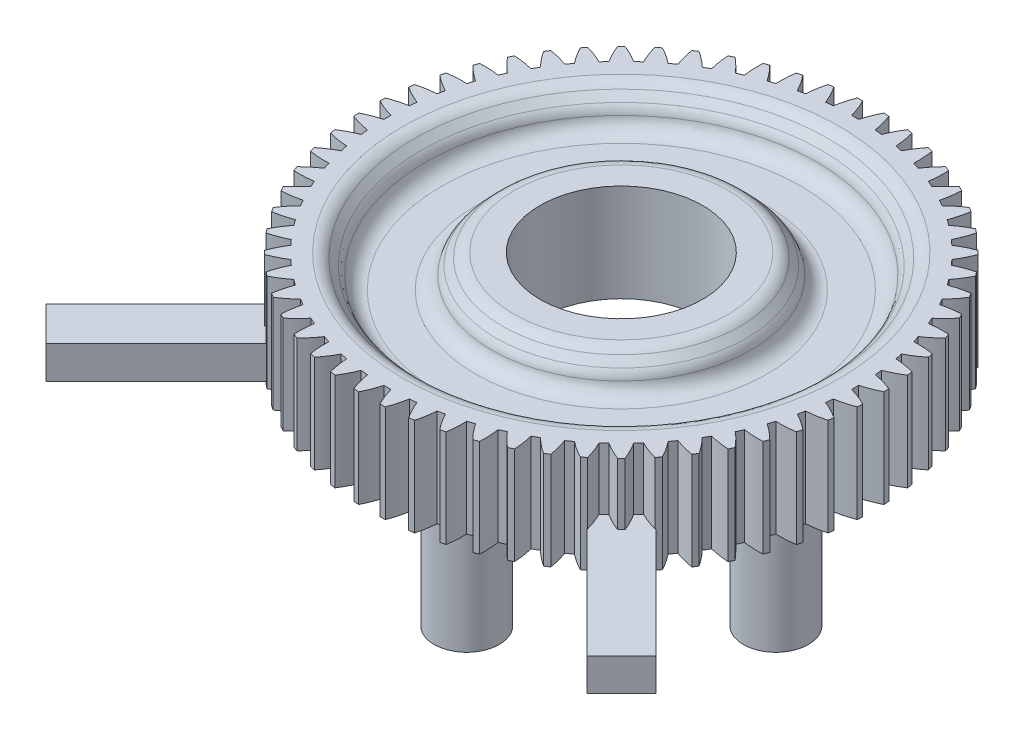
SolidWorks part; units mm, degrees
ref_plane "Front" through (0, 0, 0) normal (0, 0, 1) x (1, 0, 0)
ref_plane "Top" through (0, 0, 0) normal (0, 1, 0) x (1, 0, 0)
ref_plane "Right" through (0, 0, 0) normal (1, 0, 0) x (0, 0, -1)
sketch "Sketch1" plane through (0, 0, 0) normal (0, 1, 0) x (1, 0, 0)
  arc A240 (-0.2149, 14.3725) -> (-0.65, 15.4864) centre (-5.9935, 12.7577) ccw
  arc A241 (-0.65, 15.4864) -> (-0.9723, 15.4695) centre (0, 0.0001) ccw
  arc A242 (-0.9723, 15.4695) -> (-1.2885, 14.3162) centre (4.6272, 13.3143) ccw
  arc A243 (-1.2885, 14.3162) -> (-1.7161, 14.2713) centre (0, 0.0001) ccw
  arc A244 (-1.7161, 14.2713) -> (-2.2652, 15.3337) centre (-7.2942, 12.0613) ccw
  arc A245 (-2.2652, 15.3337) -> (-2.584, 15.2832) centre (0, 0.0001) ccw
  arc A246 (-2.584, 15.2832) -> (-2.7779, 14.1031) centre (3.2101, 13.725) ccw
  arc A247 (-2.7779, 14.1031) -> (-3.1984, 14.0137) centre (0, 0.0001) ccw
  arc A248 (-3.1984, 14.0137) -> (-3.8555, 15.0129) centre (-8.515, 11.2328) ccw
  arc A249 (-3.8555, 15.0129) -> (-4.1674, 14.9293) centre (0, 0.0001) ccw
  arc A250 (-4.1674, 14.9293) -> (-4.2369, 13.7354) centre (1.7579, 13.9854) ccw
  arc A251 (-4.2369, 13.7354) -> (-4.6457, 13.6026) centre (0, 0.0001) ccw
  arc A252 (-4.6457, 13.6026) -> (-5.4037, 14.5276) centre (-9.6425, 10.2812) ccw
  arc A253 (-5.4037, 14.5276) -> (-5.7051, 14.4119) centre (0, 0.0001) ccw
  arc A254 (-5.7051, 14.4119) -> (-5.6494, 13.2173) centre (0.2864, 14.0925) ccw
  arc A255 (-5.6494, 13.2173) -> (-6.0421, 13.0425) centre (0, 0.0001) ccw
  arc A256 (-6.0421, 13.0425) -> (-6.8926, 13.8832) centre (-10.6644, 9.2169) ccw
  arc A257 (-6.8926, 13.8832) -> (-7.1803, 13.7366) centre (0, 0.0001) ccw
  arc A258 (-7.1803, 13.7366) -> (-7, 12.5544) centre (-1.1882, 14.0453) ccw
  arc A259 (-7, 12.5544) -> (-7.3723, 12.3395) centre (0, 0.0001) ccw
  arc A260 (-7.3723, 12.3395) -> (-8.3061, 13.0867) centre (-11.5694, 8.0517) ccw
  arc A261 (-8.3061, 13.0867) -> (-8.5768, 12.9108) centre (0, 0.0001) ccw
  arc A262 (-8.5768, 12.9108) -> (-8.274, 11.7539) centre (-2.6498, 13.8441) ccw
  arc A263 (-8.274, 11.7539) -> (-8.6218, 11.5012) centre (0, 0.0001) ccw
  arc A264 (-8.6218, 11.5012) -> (-9.6285, 12.1468) centre (-12.3476, 6.7983) ccw
  arc A265 (-9.6285, 12.1468) -> (-9.8794, 11.9436) centre (0, 0.0001) ccw
  arc A266 (-9.8794, 11.9436) -> (-9.4573, 10.8247) centre (-4.0824, 13.4913) ccw
  arc A267 (-9.4573, 10.8247) -> (-9.7767, 10.537) centre (0, 0.0001) ccw
  arc A268 (-9.7767, 10.537) -> (-10.8454, 11.0738) centre (-12.9906, 5.4704) ccw
  arc A269 (-10.8454, 11.0738) -> (-11.0737, 10.8455) centre (0, 0.0001) ccw
  arc A270 (-11.0737, 10.8455) -> (-10.5369, 9.7768) centre (-5.4703, 12.9907) ccw
  arc A271 (-10.5369, 9.7768) -> (-10.8246, 9.4573) centre (0, 0.0001) ccw
  arc A272 (-10.8246, 9.4573) -> (-11.9435, 9.8794) centre (-13.4912, 4.0825) ccw
  arc A273 (-11.9435, 9.8794) -> (-12.1467, 9.6286) centre (0, 0.0001) ccw
  arc A274 (-12.1467, 9.6286) -> (-11.5012, 8.6218) centre (-6.7982, 12.3477) ccw
  arc A275 (-11.5012, 8.6218) -> (-11.7538, 8.2741) centre (0, 0.0001) ccw
  arc A276 (-11.7538, 8.2741) -> (-12.9108, 8.5769) centre (-13.8441, 2.6499) ccw
  arc A277 (-12.9108, 8.5769) -> (-13.0866, 8.3061) centre (0, 0.0001) ccw
  arc A278 (-13.0866, 8.3061) -> (-12.3394, 7.3724) centre (-8.0516, 11.5695) ccw
  arc A279 (-12.3394, 7.3724) -> (-12.5543, 7.0001) centre (0, 0.0001) ccw
  arc A280 (-12.5543, 7.0001) -> (-13.7366, 7.1804) centre (-14.0452, 1.1883) ccw
  arc A281 (-13.7366, 7.1804) -> (-13.8831, 6.8927) centre (0, 0.0001) ccw
  arc A282 (-13.8831, 6.8927) -> (-13.0424, 6.0422) centre (-9.2169, 10.6645) ccw
  arc A283 (-13.0424, 6.0422) -> (-13.2172, 5.6495) centre (0, 0.0001) ccw
  arc A284 (-13.2172, 5.6495) -> (-14.4118, 5.7052) centre (-14.0925, -0.2863) ccw
  arc A285 (-14.4118, 5.7052) -> (-14.5275, 5.4038) centre (0, 0.0001) ccw
  arc A286 (-14.5275, 5.4038) -> (-13.6025, 4.6458) centre (-10.2811, 9.6426) ccw
  arc A287 (-13.6025, 4.6458) -> (-13.7354, 4.237) centre (0, 0.0001) ccw
  arc A288 (-13.7354, 4.237) -> (-14.9292, 4.1675) centre (-13.9853, -1.7578) ccw
  arc A289 (-14.9292, 4.1675) -> (-15.0128, 3.8556) centre (0, 0.0001) ccw
  arc A290 (-15.0128, 3.8556) -> (-14.0136, 3.1985) centre (-11.2327, 8.5151) ccw
  arc A291 (-14.0136, 3.1985) -> (-14.103, 2.778) centre (0, 0.0001) ccw
  arc A292 (-14.103, 2.778) -> (-15.2831, 2.5841) centre (-13.725, -3.2101) ccw
  arc A293 (-15.2831, 2.5841) -> (-15.3336, 2.2652) centre (0, 0.0001) ccw
  arc A294 (-15.3336, 2.2652) -> (-14.2712, 1.7161) centre (-12.0612, 7.2943) ccw
  arc A295 (-14.2712, 1.7161) -> (-14.3161, 1.2886) centre (0, 0.0001) ccw
  arc A296 (-14.3161, 1.2886) -> (-15.4695, 0.9724) centre (-13.3142, -4.6271) ccw
  arc A297 (-15.4695, 0.9724) -> (-15.4863, 0.65) centre (0, 0.0001) ccw
  arc A298 (-15.4863, 0.65) -> (-14.3724, 0.215) centre (-12.7576, 5.9936) ccw
  arc A299 (-14.3724, 0.215) -> (-14.3724, -0.2149) centre (0, 0.0001) ccw
  arc A300 (-14.3724, -0.2149) -> (-15.4863, -0.6499) centre (-12.7576, -5.9935) ccw
  arc A301 (-15.4863, -0.6499) -> (-15.4695, -0.9723) centre (0, 0.0001) ccw
  arc A302 (-15.4695, -0.9723) -> (-14.3161, -1.2885) centre (-13.3142, 4.6273) ccw
  arc A303 (-14.3161, -1.2885) -> (-14.2712, -1.716) centre (0, 0.0001) ccw
  arc A304 (-14.2712, -1.716) -> (-15.3336, -2.2651) centre (-12.0612, -7.2942) ccw
  arc A305 (-15.3336, -2.2651) -> (-15.2831, -2.584) centre (0, 0.0001) ccw
  arc A306 (-15.2831, -2.584) -> (-14.103, -2.7779) centre (-13.725, 3.2102) ccw
  arc A307 (-14.103, -2.7779) -> (-14.0136, -3.1984) centre (0, 0.0001) ccw
  arc A308 (-14.0136, -3.1984) -> (-15.0128, -3.8555) centre (-11.2327, -8.515) ccw
  arc A309 (-15.0128, -3.8555) -> (-14.9292, -4.1673) centre (0, 0.0001) ccw
  arc A310 (-14.9292, -4.1673) -> (-13.7354, -4.2368) centre (-13.9853, 1.758) ccw
  arc A311 (-13.7354, -4.2368) -> (-13.6025, -4.6457) centre (0, 0.0001) ccw
  arc A312 (-13.6025, -4.6457) -> (-14.5275, -5.4036) centre (-10.2811, -9.6425) ccw
  arc A313 (-14.5275, -5.4036) -> (-14.4118, -5.705) centre (0, 0.0001) ccw
  arc A314 (-14.4118, -5.705) -> (-13.2172, -5.6494) centre (-14.0925, 0.2865) ccw
  arc A315 (-13.2172, -5.6494) -> (-13.0424, -6.0421) centre (0, 0.0001) ccw
  arc A316 (-13.0424, -6.0421) -> (-13.8831, -6.8926) centre (-9.2169, -10.6643) ccw
  arc A317 (-13.8831, -6.8926) -> (-13.7366, -7.1802) centre (0, 0.0001) ccw
  arc A318 (-13.7366, -7.1802) -> (-12.5543, -7) centre (-14.0452, -1.1882) ccw
  arc A319 (-12.5543, -7) -> (-12.3394, -7.3723) centre (0, 0.0001) ccw
  arc A320 (-12.3394, -7.3723) -> (-13.0866, -8.306) centre (-8.0516, -11.5693) ccw
  arc A321 (-13.0866, -8.306) -> (-12.9108, -8.5768) centre (0, 0.0001) ccw
  arc A322 (-12.9108, -8.5768) -> (-11.7538, -8.2739) centre (-13.8441, -2.6498) ccw
  arc A323 (-11.7538, -8.2739) -> (-11.5012, -8.6217) centre (0, 0.0001) ccw
  arc A324 (-11.5012, -8.6217) -> (-12.1467, -9.6284) centre (-6.7982, -12.3476) ccw
  arc A325 (-12.1467, -9.6284) -> (-11.9435, -9.8793) centre (0, 0.0001) ccw
  arc A326 (-11.9435, -9.8793) -> (-10.8246, -9.4572) centre (-13.4912, -4.0824) ccw
  arc A327 (-10.8246, -9.4572) -> (-10.5369, -9.7767) centre (0, 0.0001) ccw
  arc A328 (-10.5369, -9.7767) -> (-11.0737, -10.8454) centre (-5.4703, -12.9905) ccw
  arc A329 (-11.0737, -10.8454) -> (-10.8454, -11.0736) centre (0, 0.0001) ccw
  arc A330 (-10.8454, -11.0736) -> (-9.7767, -10.5369) centre (-12.9906, -5.4702) ccw
  arc A331 (-9.7767, -10.5369) -> (-9.4573, -10.8245) centre (0, 0.0001) ccw
  arc A332 (-9.4573, -10.8245) -> (-9.8794, -11.9435) centre (-4.0824, -13.4912) ccw
  arc A333 (-9.8794, -11.9435) -> (-9.6285, -12.1466) centre (0, 0.0001) ccw
  arc A334 (-9.6285, -12.1466) -> (-8.6218, -11.5011) centre (-12.3476, -6.7981) ccw
  arc A335 (-8.6218, -11.5011) -> (-8.274, -11.7538) centre (0, 0.0001) ccw
  arc A336 (-8.274, -11.7538) -> (-8.5768, -12.9107) centre (-2.6498, -13.844) ccw
  arc A337 (-8.5768, -12.9107) -> (-8.3061, -13.0865) centre (0, 0.0001) ccw
  arc A338 (-8.3061, -13.0865) -> (-7.3723, -12.3393) centre (-11.5694, -8.0516) ccw
  arc A339 (-7.3723, -12.3393) -> (-7, -12.5543) centre (0, 0.0001) ccw
  arc A340 (-7, -12.5543) -> (-7.1803, -13.7365) centre (-1.1882, -14.0452) ccw
  arc A341 (-7.1803, -13.7365) -> (-6.8926, -13.8831) centre (0, 0.0001) ccw
  arc A342 (-6.8926, -13.8831) -> (-6.0421, -13.0423) centre (-10.6644, -9.2168) ccw
  arc A343 (-6.0421, -13.0423) -> (-5.6494, -13.2172) centre (0, 0.0001) ccw
  arc A344 (-5.6494, -13.2172) -> (-5.7051, -14.4118) centre (0.2864, -14.0924) ccw
  arc A345 (-5.7051, -14.4118) -> (-5.4037, -14.5275) centre (0, 0.0001) ccw
  arc A346 (-5.4037, -14.5275) -> (-4.6457, -13.6025) centre (-9.6425, -10.281) ccw
  arc A347 (-4.6457, -13.6025) -> (-4.2369, -13.7353) centre (0, 0.0001) ccw
  arc A348 (-4.2369, -13.7353) -> (-4.1674, -14.9292) centre (1.7579, -13.9853) ccw
  arc A349 (-4.1674, -14.9292) -> (-3.8555, -15.0127) centre (0, 0.0001) ccw
  arc A350 (-3.8555, -15.0127) -> (-3.1984, -14.0136) centre (-8.515, -11.2326) ccw
  arc A351 (-3.1984, -14.0136) -> (-2.7779, -14.1029) centre (0, 0.0001) ccw
  arc A352 (-2.7779, -14.1029) -> (-2.584, -15.283) centre (3.2101, -13.7249) ccw
  arc A353 (-2.584, -15.283) -> (-2.2652, -15.3335) centre (0, 0.0001) ccw
  arc A354 (-2.2652, -15.3335) -> (-1.7161, -14.2711) centre (-7.2942, -12.0612) ccw
  arc A355 (-1.7161, -14.2711) -> (-1.2885, -14.3161) centre (0, 0.0001) ccw
  arc A356 (-1.2885, -14.3161) -> (-0.9723, -15.4694) centre (4.6272, -13.3142) ccw
  arc A357 (-0.9723, -15.4694) -> (-0.65, -15.4863) centre (0, 0.0001) ccw
  arc A358 (-0.65, -15.4863) -> (-0.2149, -14.3723) centre (-5.9935, -12.7576) ccw
  arc A359 (-0.2149, -14.3723) -> (0.215, -14.3723) centre (0, 0.0001) ccw
  arc A360 (0.215, -14.3723) -> (0.65, -15.4863) centre (5.9936, -12.7576) ccw
  arc A361 (0.65, -15.4863) -> (0.9724, -15.4694) centre (0, 0.0001) ccw
  arc A362 (0.9724, -15.4694) -> (1.2886, -14.3161) centre (-4.6272, -13.3142) ccw
  arc A363 (1.2886, -14.3161) -> (1.7161, -14.2711) centre (0, 0.0001) ccw
  arc A364 (1.7161, -14.2711) -> (2.2652, -15.3335) centre (7.2943, -12.0612) ccw
  arc A365 (2.2652, -15.3335) -> (2.584, -15.283) centre (0, 0.0001) ccw
  arc A366 (2.584, -15.283) -> (2.778, -14.1029) centre (-3.2101, -13.7249) ccw
  arc A367 (2.778, -14.1029) -> (3.1984, -14.0136) centre (0, 0.0001) ccw
  arc A368 (3.1984, -14.0136) -> (3.8556, -15.0127) centre (8.5151, -11.2326) ccw
  arc A369 (3.8556, -15.0127) -> (4.1674, -14.9292) centre (0, 0.0001) ccw
  arc A370 (4.1674, -14.9292) -> (4.2369, -13.7353) centre (-1.7579, -13.9853) ccw
  arc A371 (4.2369, -13.7353) -> (4.6457, -13.6025) centre (0, 0.0001) ccw
  arc A372 (4.6457, -13.6025) -> (5.4037, -14.5275) centre (9.6426, -10.281) ccw
  arc A373 (5.4037, -14.5275) -> (5.7051, -14.4118) centre (0, 0.0001) ccw
  arc A374 (5.7051, -14.4118) -> (5.6494, -13.2172) centre (-0.2864, -14.0924) ccw
  arc A375 (5.6494, -13.2172) -> (6.0422, -13.0423) centre (0, 0.0001) ccw
  arc A376 (6.0422, -13.0423) -> (6.8927, -13.8831) centre (10.6644, -9.2168) ccw
  arc A377 (6.8927, -13.8831) -> (7.1803, -13.7365) centre (0, 0.0001) ccw
  arc A378 (7.1803, -13.7365) -> (7.0001, -12.5543) centre (1.1883, -14.0452) ccw
  arc A379 (7.0001, -12.5543) -> (7.3724, -12.3393) centre (0, 0.0001) ccw
  arc A380 (7.3724, -12.3393) -> (8.3061, -13.0865) centre (11.5694, -8.0516) ccw
  arc A381 (8.3061, -13.0865) -> (8.5768, -12.9107) centre (0, 0.0001) ccw
  arc A382 (8.5768, -12.9107) -> (8.274, -11.7538) centre (2.6499, -13.844) ccw
  arc A383 (8.274, -11.7538) -> (8.6218, -11.5011) centre (0, 0.0001) ccw
  arc A384 (8.6218, -11.5011) -> (9.6285, -12.1466) centre (12.3477, -6.7981) ccw
  arc A385 (9.6285, -12.1466) -> (9.8794, -11.9435) centre (0, 0.0001) ccw
  arc A386 (9.8794, -11.9435) -> (9.4573, -10.8245) centre (4.0825, -13.4912) ccw
  arc A387 (9.4573, -10.8245) -> (9.7768, -10.5369) centre (0, 0.0001) ccw
  arc A388 (9.7768, -10.5369) -> (10.8454, -11.0736) centre (12.9906, -5.4702) ccw
  arc A389 (10.8454, -11.0736) -> (11.0737, -10.8454) centre (0, 0.0001) ccw
  arc A390 (11.0737, -10.8454) -> (10.537, -9.7767) centre (5.4703, -12.9905) ccw
  arc A391 (10.537, -9.7767) -> (10.8246, -9.4572) centre (0, 0.0001) ccw
  arc A392 (10.8246, -9.4572) -> (11.9435, -9.8793) centre (13.4913, -4.0824) ccw
  arc A393 (11.9435, -9.8793) -> (12.1467, -9.6284) centre (0, 0.0001) ccw
  arc A394 (12.1467, -9.6284) -> (11.5012, -8.6217) centre (6.7982, -12.3476) ccw
  arc A395 (11.5012, -8.6217) -> (11.7539, -8.2739) centre (0, 0.0001) ccw
  arc A396 (11.7539, -8.2739) -> (12.9108, -8.5768) centre (13.8441, -2.6498) ccw
  arc A397 (12.9108, -8.5768) -> (13.0866, -8.306) centre (0, 0.0001) ccw
  arc A398 (13.0866, -8.306) -> (12.3394, -7.3723) centre (8.0517, -11.5693) ccw
  arc A399 (12.3394, -7.3723) -> (12.5543, -7) centre (0, 0.0001) ccw
  arc A400 (12.5543, -7) -> (13.7366, -7.1802) centre (14.0452, -1.1882) ccw
  arc A401 (13.7366, -7.1802) -> (13.8832, -6.8926) centre (0, 0.0001) ccw
  arc A402 (13.8832, -6.8926) -> (13.0424, -6.0421) centre (9.2169, -10.6643) ccw
  arc A403 (13.0424, -6.0421) -> (13.2173, -5.6494) centre (0, 0.0001) ccw
  arc A404 (13.2173, -5.6494) -> (14.4119, -5.705) centre (14.0925, 0.2865) ccw
  arc A405 (14.4119, -5.705) -> (14.5276, -5.4036) centre (0, 0.0001) ccw
  arc A406 (14.5276, -5.4036) -> (13.6026, -4.6457) centre (10.2811, -9.6425) ccw
  arc A407 (13.6026, -4.6457) -> (13.7354, -4.2368) centre (0, 0.0001) ccw
  arc A408 (13.7354, -4.2368) -> (14.9293, -4.1673) centre (13.9854, 1.758) ccw
  arc A409 (14.9293, -4.1673) -> (15.0128, -3.8555) centre (0, 0.0001) ccw
  arc A410 (15.0128, -3.8555) -> (14.0137, -3.1984) centre (11.2327, -8.515) ccw
  arc A411 (14.0137, -3.1984) -> (14.103, -2.7779) centre (0, 0.0001) ccw
  arc A412 (14.103, -2.7779) -> (15.2831, -2.584) centre (13.725, 3.2102) ccw
  arc A413 (15.2831, -2.584) -> (15.3336, -2.2651) centre (0, 0.0001) ccw
  arc A414 (15.3336, -2.2651) -> (14.2712, -1.716) centre (12.0613, -7.2942) ccw
  arc A415 (14.2712, -1.716) -> (14.3161, -1.2885) centre (0, 0.0001) ccw
  arc A416 (14.3161, -1.2885) -> (15.4695, -0.9723) centre (13.3143, 4.6273) ccw
  arc A417 (15.4695, -0.9723) -> (15.4864, -0.6499) centre (0, 0.0001) ccw
  arc A418 (15.4864, -0.6499) -> (14.3724, -0.2149) centre (12.7576, -5.9935) ccw
  arc A419 (14.3724, -0.2149) -> (14.3724, 0.215) centre (0, 0.0001) ccw
  arc A420 (14.3724, 0.215) -> (15.4864, 0.65) centre (12.7576, 5.9936) ccw
  arc A421 (15.4864, 0.65) -> (15.4695, 0.9724) centre (0, 0.0001) ccw
  arc A422 (15.4695, 0.9724) -> (14.3161, 1.2886) centre (13.3143, -4.6271) ccw
  arc A423 (14.3161, 1.2886) -> (14.2712, 1.7161) centre (0, 0.0001) ccw
  arc A424 (14.2712, 1.7161) -> (15.3336, 2.2652) centre (12.0613, 7.2943) ccw
  arc A425 (15.3336, 2.2652) -> (15.2831, 2.5841) centre (0, 0.0001) ccw
  arc A426 (15.2831, 2.5841) -> (14.103, 2.778) centre (13.725, -3.2101) ccw
  arc A427 (14.103, 2.778) -> (14.0137, 3.1985) centre (0, 0.0001) ccw
  arc A428 (14.0137, 3.1985) -> (15.0128, 3.8556) centre (11.2327, 8.5151) ccw
  arc A429 (15.0128, 3.8556) -> (14.9293, 4.1675) centre (0, 0.0001) ccw
  arc A430 (14.9293, 4.1675) -> (13.7354, 4.237) centre (13.9854, -1.7578) ccw
  arc A431 (13.7354, 4.237) -> (13.6026, 4.6458) centre (0, 0.0001) ccw
  arc A432 (13.6026, 4.6458) -> (14.5276, 5.4038) centre (10.2811, 9.6426) ccw
  arc A433 (14.5276, 5.4038) -> (14.4119, 5.7052) centre (0, 0.0001) ccw
  arc A434 (14.4119, 5.7052) -> (13.2173, 5.6495) centre (14.0925, -0.2863) ccw
  arc A435 (13.2173, 5.6495) -> (13.0424, 6.0422) centre (0, 0.0001) ccw
  arc A436 (13.0424, 6.0422) -> (13.8832, 6.8927) centre (9.2169, 10.6645) ccw
  arc A437 (13.8832, 6.8927) -> (13.7366, 7.1804) centre (0, 0.0001) ccw
  arc A438 (13.7366, 7.1804) -> (12.5543, 7.0001) centre (14.0452, 1.1883) ccw
  arc A439 (12.5543, 7.0001) -> (12.3394, 7.3724) centre (0, 0.0001) ccw
  arc A440 (12.3394, 7.3724) -> (13.0866, 8.3061) centre (8.0517, 11.5695) ccw
  arc A441 (13.0866, 8.3061) -> (12.9108, 8.5769) centre (0, 0.0001) ccw
  arc A442 (12.9108, 8.5769) -> (11.7539, 8.2741) centre (13.8441, 2.6499) ccw
  arc A443 (11.7539, 8.2741) -> (11.5012, 8.6218) centre (0, 0.0001) ccw
  arc A444 (11.5012, 8.6218) -> (12.1467, 9.6286) centre (6.7982, 12.3477) ccw
  arc A445 (12.1467, 9.6286) -> (11.9435, 9.8794) centre (0, 0.0001) ccw
  arc A446 (11.9435, 9.8794) -> (10.8246, 9.4573) centre (13.4913, 4.0825) ccw
  arc A447 (10.8246, 9.4573) -> (10.537, 9.7768) centre (0, 0.0001) ccw
  arc A448 (10.537, 9.7768) -> (11.0737, 10.8455) centre (5.4703, 12.9907) ccw
  arc A449 (11.0737, 10.8455) -> (10.8454, 11.0738) centre (0, 0.0001) ccw
  arc A450 (10.8454, 11.0738) -> (9.7768, 10.537) centre (12.9906, 5.4704) ccw
  arc A451 (9.7768, 10.537) -> (9.4573, 10.8247) centre (0, 0.0001) ccw
  arc A452 (9.4573, 10.8247) -> (9.8794, 11.9436) centre (4.0825, 13.4913) ccw
  arc A453 (9.8794, 11.9436) -> (9.6285, 12.1468) centre (0, 0.0001) ccw
  arc A454 (9.6285, 12.1468) -> (8.6218, 11.5012) centre (12.3477, 6.7983) ccw
  arc A455 (8.6218, 11.5012) -> (8.274, 11.7539) centre (0, 0.0001) ccw
  arc A456 (8.274, 11.7539) -> (8.5768, 12.9108) centre (2.6499, 13.8441) ccw
  arc A457 (8.5768, 12.9108) -> (8.3061, 13.0867) centre (0, 0.0001) ccw
  arc A458 (8.3061, 13.0867) -> (7.3724, 12.3395) centre (11.5694, 8.0517) ccw
  arc A459 (7.3724, 12.3395) -> (7.0001, 12.5544) centre (0, 0.0001) ccw
  arc A460 (7.0001, 12.5544) -> (7.1803, 13.7366) centre (1.1883, 14.0453) ccw
  arc A461 (7.1803, 13.7366) -> (6.8927, 13.8832) centre (0, 0.0001) ccw
  arc A462 (6.8927, 13.8832) -> (6.0422, 13.0425) centre (10.6644, 9.2169) ccw
  arc A463 (6.0422, 13.0425) -> (5.6494, 13.2173) centre (0, 0.0001) ccw
  arc A464 (5.6494, 13.2173) -> (5.7051, 14.4119) centre (-0.2864, 14.0925) ccw
  arc A465 (5.7051, 14.4119) -> (5.4037, 14.5276) centre (0, 0.0001) ccw
  arc A466 (5.4037, 14.5276) -> (4.6457, 13.6026) centre (9.6426, 10.2812) ccw
  arc A467 (4.6457, 13.6026) -> (4.2369, 13.7354) centre (0, 0.0001) ccw
  arc A468 (4.2369, 13.7354) -> (4.1674, 14.9293) centre (-1.7579, 13.9854) ccw
  arc A469 (4.1674, 14.9293) -> (3.8556, 15.0129) centre (0, 0.0001) ccw
  arc A470 (3.8556, 15.0129) -> (3.1984, 14.0137) centre (8.5151, 11.2328) ccw
  arc A471 (3.1984, 14.0137) -> (2.778, 14.1031) centre (0, 0.0001) ccw
  arc A472 (2.778, 14.1031) -> (2.584, 15.2832) centre (-3.2101, 13.725) ccw
  arc A473 (2.584, 15.2832) -> (2.2652, 15.3337) centre (0, 0.0001) ccw
  arc A474 (2.2652, 15.3337) -> (1.7161, 14.2713) centre (7.2943, 12.0613) ccw
  arc A475 (1.7161, 14.2713) -> (1.2886, 14.3162) centre (0, 0.0001) ccw
  arc A476 (1.2886, 14.3162) -> (0.9724, 15.4695) centre (-4.6272, 13.3143) ccw
  arc A477 (0.9724, 15.4695) -> (0.65, 15.4864) centre (0, 0.0001) ccw
  arc A478 (0.65, 15.4864) -> (0.215, 14.3725) centre (5.9936, 12.7577) ccw
  arc A479 (0.215, 14.3725) -> (-0.2149, 14.3725) centre (0, 0.0001) ccw
extrude "Boss-Extrude1" add sketch "Sketch1" along normal blind 6
sketch "Sketch2" plane through (0, 6, 0) normal (0, 1, 0) x (1, 0, 0)
  circle A0 centre (0, 0) radius 5
extrude "Cut-Extrude2" cut sketch "Sketch2" against normal blind 6 contours A0
sketch "Sketch3" plane through (0, 6, 0) normal (0, 1, 0) x (1, 0, 0)
  circle A0 centre (0, 0) radius 8
  circle A1 centre (0, 0) radius 12
extrude "Cut-Extrude3" cut sketch "Sketch3" against normal blind 2
chamfer "Chamfer1" distance 1 angle 45 1 edges at (0, 6, 12)
chamfer "Chamfer2" distance 1 angle 45 1 edges at (0, 6, 8)
fillet "Fillet1" radius 1 1 edges at (0, 6, 13)
fillet "Fillet2" radius 1 1 edges at (0, 5, 12)
fillet "Fillet3" radius 1 1 edges at (0, 6, 7)
fillet "Fillet4" radius 1 1 edges at (0, 5, 8)
sketch "Sketch4" plane through (0, 0, 0) normal (0, -1, 0) x (1, 0, 0)
  circle A0 centre (-9.5, 0) radius 2
  circle A1 centre (0, -9.5) radius 2
  circle A2 centre (9.5, 0) radius 2
  circle A3 centre (0, 9.5) radius 2
extrude "Boss-Extrude2" add sketch "Sketch4" along normal blind 9.12
fillet "Fillet5" radius 1 1 edges at (0, 4, 12)
fillet "Fillet6" radius 1 1 edges at (0, 4, 8)
sketch "Sketch5" plane through (0, -9.12, 0) normal (0, -1, 0) x (1, 0, 0)
  circle A0 centre (-9.5, 0) radius 1.1
extrude "Cut-Extrude4" cut sketch "Sketch5" against normal blind 8
sketch "Sketch6" plane through (0, -9.12, 0) normal (0, -1, 0) x (1, 0, 0)
  circle A0 centre (0, 9.5) radius 1.1
sketch "Sketch7" plane through (0, -9.12, 0) normal (0, -1, 0) x (1, 0, 0)
  circle A0 centre (0, -9.5) radius 1.1
sketch "Sketch8" plane through (0, -9.12, 0) normal (0, -1, 0) x (1, 0, 0)
  circle A0 centre (9.5, 0) radius 1.1
extrude "Cut-Extrude5" cut sketch "Sketch6" against normal blind 8
extrude "Cut-Extrude6" cut sketch "Sketch8" against normal blind 8
extrude "Cut-Extrude7" cut sketch "Sketch7" against normal blind 8
sketch "Sketch9" plane through (0, 0, 0) normal (0, -1, 0) x (1, 0, 0)
  point P10 (-3.5355, 3.5355)
  point P11 (3.5355, 3.5355)
ref_plane "Plane1" through (3.5355, 0, 3.5355) normal (-0.7071, 0, -0.7071) x (-0.7071, 0, 0.7071)
ref_plane "Plane2" through (-3.5355, 0, 3.5355) normal (0.7071, 0, -0.7071) x (-0.7071, 0, -0.7071)
sketch "Sketch10" plane through (-3.5355, 0, 3.5355) normal (0.7071, 0, -0.7071) x (-0.7071, 0, -0.7071)
  line L6 (1.5, 2.2) -> (-1.5, 2.2)
  line L7 (1.5, 2.2) -> (1.5, 0.2)
  line L8 (1.5, 0.2) -> (-1.5, 0.2)
  line L9 (-1.5, 2.2) -> (-1.5, 0.2)
extrude "Boss-Extrude3" add sketch "Sketch10" against normal blind 20
sketch "Sketch11" plane through (3.5355, 0, 3.5355) normal (-0.7071, 0, -0.7071) x (-0.7071, 0, 0.7071)
  line L4 (-1.5, 0.2) -> (1.5, 0.2)
  line L5 (-1.5, 0.2) -> (-1.5, 2.2)
  line L6 (-1.5, 2.2) -> (1.5, 2.2)
  line L7 (1.5, 0.2) -> (1.5, 2.2)
extrude "Boss-Extrude4" add sketch "Sketch11" against normal blind 20
